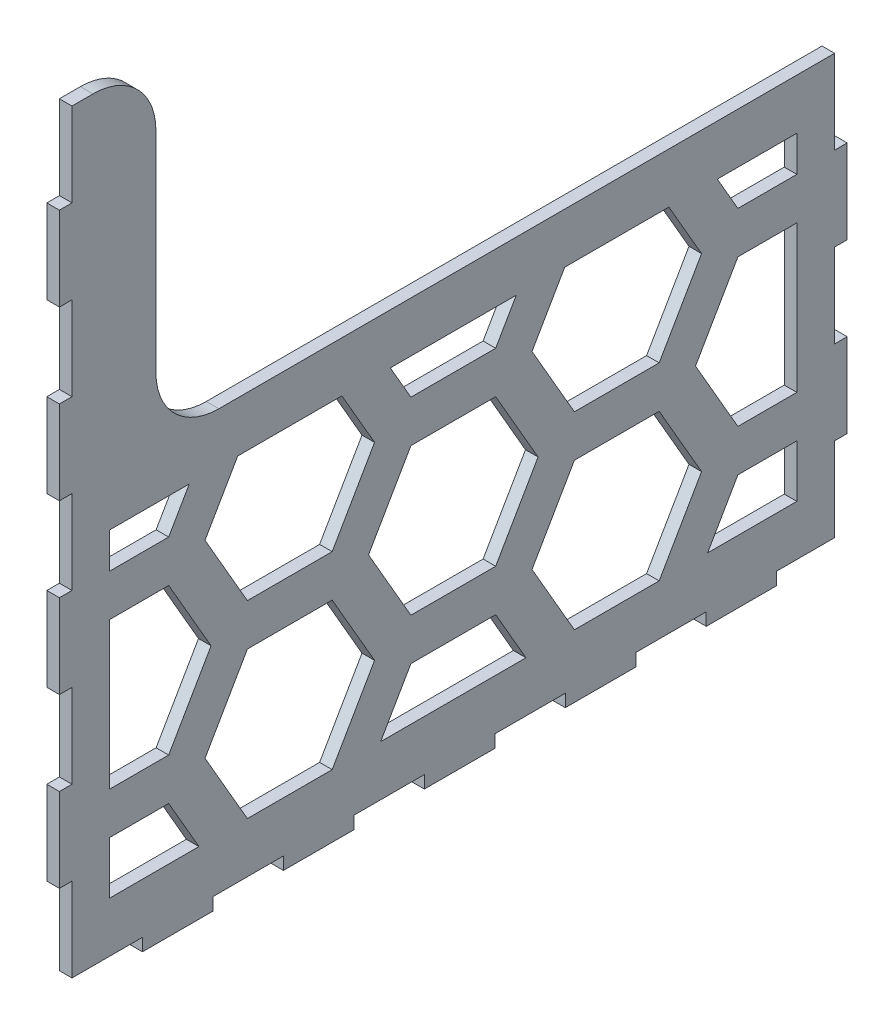
SolidWorks part; units mm, degrees
ref_plane "Front Plane" through (0, 0, 0) normal (0, 0, 1) x (1, 0, 0)
ref_plane "Top Plane" through (0, 0, 0) normal (0, 1, 0) x (1, 0, 0)
ref_plane "Right Plane" through (0, 0, 0) normal (1, 0, 0) x (0, 0, -1)
sketch "Sketch1" plane through (0, 0, 0) normal (1, 0, 0) x (0, 0, -1)
  line L1 (-90.8886, -90) -> (90.8886, -90)
  line L2 (-90.8886, -90) -> (-90.8886, 90)
  line L3 (-90.8886, 90) -> (90.8886, 90)
  line L4 (90.8886, -90) -> (90.8886, 90)
  line L5 (-90.8886, -90) -> (90.8886, 90) construction
  line L6 (-90.8886, 90) -> (90.8886, -90) construction
  point P0 (0, 0)
  dimension "D1" = 181.7773
  dimension "D2" = 180
extrude "Boss-Extrude1" add sketch "Sketch1" along normal blind 3
sketch "Sketch2" plane through (3, 0, 0) normal (1, 0, 0) x (0, 0, -1)
  line L0 (-90.8886, -90) -> (90.8886, -90) construction
  line L1 (-74.0907, -93) -> (-57.2928, -93)
  line L2 (-74.0907, -93) -> (-74.0907, -90)
  line L3 (-74.0907, -90) -> (-57.2928, -90)
  line L4 (-57.2928, -93) -> (-57.2928, -90)
  line L5 (-74.0907, -93) -> (-57.2928, -90) construction
  line L6 (-74.0907, -90) -> (-57.2928, -93) construction
  line L7 (-90.8886, -93) -> (-74.0907, -93) construction
  line L8 (-40.4948, -93) -> (-23.6969, -93)
  line L9 (-40.4948, -93) -> (-40.4948, -90)
  line L10 (-40.4948, -90) -> (-23.6969, -90)
  line L11 (-23.6969, -93) -> (-23.6969, -90)
  line L12 (-40.4948, -93) -> (-23.6969, -90) construction
  line L13 (-40.4948, -90) -> (-23.6969, -93) construction
  line L14 (-6.899, -93) -> (9.899, -93)
  line L15 (-6.899, -93) -> (-6.899, -90)
  line L16 (-6.899, -90) -> (9.899, -90)
  line L17 (9.899, -93) -> (9.899, -90)
  line L18 (-6.899, -93) -> (9.899, -90) construction
  line L19 (-6.899, -90) -> (9.899, -93) construction
  line L20 (-57.2928, -93) -> (-40.4948, -93) construction
  line L21 (-23.6969, -93) -> (-6.899, -93) construction
  line L22 (9.899, -93) -> (26.6969, -93) construction
  line L24 (90.8886, -90) -> (90.8886, 90) construction
  line L25 (93.8886, -70) -> (90.8887, -70)
  line L26 (93.8886, -70) -> (93.8886, -50)
  line L27 (93.8886, -50) -> (90.8886, -50)
  line L28 (90.8887, -70) -> (90.8886, -50)
  line L29 (93.8886, -70) -> (90.8886, -50) construction
  line L30 (93.8886, -50) -> (90.8887, -70) construction
  line L31 (93.8886, 90) -> (93.8886, 70) construction
  line L32 (93.8887, -30) -> (90.8886, -30)
  line L33 (93.8887, -30) -> (93.8886, -10)
  line L34 (93.8886, -10) -> (90.8886, -10)
  line L35 (90.8886, -30) -> (90.8886, -10)
  line L36 (93.8887, -30) -> (90.8886, -10) construction
  line L37 (93.8886, -10) -> (90.8886, -30) construction
  line L38 (93.8887, 10) -> (90.8886, 10)
  line L39 (93.8887, 10) -> (93.8887, 30)
  line L40 (93.8887, 30) -> (90.8886, 30)
  line L41 (90.8886, 10) -> (90.8886, 30)
  line L42 (93.8887, 10) -> (90.8886, 30) construction
  line L43 (93.8887, 30) -> (90.8886, 10) construction
  line L44 (93.8886, 50) -> (90.8886, 50)
  line L45 (93.8886, 50) -> (93.8886, 70)
  line L46 (93.8886, 70) -> (90.8886, 70)
  line L47 (90.8886, 50) -> (90.8886, 70)
  line L48 (93.8886, 50) -> (90.8886, 70) construction
  line L49 (93.8886, 70) -> (90.8886, 50) construction
  line L50 (93.8886, 50) -> (93.8887, 30) construction
  line L51 (93.8887, 10) -> (93.8886, -10) construction
  line L52 (93.8887, -30) -> (93.8886, -50) construction
  line L53 (93.8886, -70) -> (93.8887, -90) construction
  line L54 (90.8886, 90) -> (-90.8886, 90) construction
  line L55 (0, -895.4773) -> (0, 49104.5227) construction
  line L56 (-93.8886, -50) -> (-90.8886, -50)
  line L57 (-90.8887, -70) -> (-90.8886, -50)
  line L58 (-93.8886, -70) -> (-90.8887, -70)
  line L59 (-93.8886, -70) -> (-93.8886, -50)
  line L60 (-93.8886, -10) -> (-90.8886, -10)
  line L61 (-90.8886, -30) -> (-90.8886, -10)
  line L62 (-93.8887, -30) -> (-90.8886, -30)
  line L63 (-93.8887, -30) -> (-93.8886, -10)
  line L64 (-93.8887, 30) -> (-90.8886, 30)
  line L65 (-90.8886, 10) -> (-90.8886, 30)
  line L66 (-93.8887, 10) -> (-90.8886, 10)
  line L67 (-93.8887, 10) -> (-93.8887, 30)
  line L68 (-93.8886, 70) -> (-90.8886, 70)
  line L69 (-90.8886, 50) -> (-90.8886, 70)
  line L70 (-93.8886, 50) -> (-90.8886, 50)
  line L71 (-93.8886, 50) -> (-93.8886, 70)
  line L72 (43.4948, -93) -> (60.2928, -93) construction
  line L73 (43.4948, -93) -> (26.6969, -93)
  line L74 (43.4948, -93) -> (43.4948, -90)
  line L75 (43.4948, -90) -> (26.6969, -90)
  line L76 (26.6969, -93) -> (26.6969, -90)
  line L77 (43.4948, -93) -> (26.6969, -90) construction
  line L78 (43.4948, -90) -> (26.6969, -93) construction
  line L79 (77.0907, -93) -> (60.2928, -93)
  line L80 (77.0907, -93) -> (77.0907, -90)
  line L81 (77.0907, -90) -> (60.2928, -90)
  line L82 (60.2928, -93) -> (60.2928, -90)
  line L83 (77.0907, -93) -> (60.2928, -90) construction
  line L84 (77.0907, -90) -> (60.2928, -93) construction
  line L85 (77.0907, -93) -> (93.8886, -93) construction
  line L86 (-90.8886, 90) -> (-90.8886, -90) construction
  point P0 (-65.6917, -91.5)
  point P7 (-32.0959, -91.5)
  point P12 (1.5, -91.5)
  point P24 (92.3887, -60)
  point P29 (92.3887, -20)
  point P34 (92.3887, 20)
  point P39 (92.3887, 60)
  point P66 (68.6917, -91.5)
  point P75 (35.0959, -91.5)
  dimension "D2" = 3
extrude "Boss-Extrude2" add sketch "Sketch2" against normal up to surface (3 mm away) up to face at (0, 0, 0)
sketch "Sketch3" plane through (3, 0, 0) normal (1, 0, 0) x (0, 0, -1)
  line L4 (93.8887, 10) -> (-70.8886, 10)
  line L6 (-70.8887, 90) -> (93.8886, 90)
  line L7 (93.8886, 90) -> (93.8887, 10)
  line L8 (93.8886, 50) -> (93.8886, 70) construction
  line L9 (90.8886, 10) -> (93.8887, 10) construction
  line L10 (90.8886, 90) -> (-90.8886, 90) construction
  line L11 (-70.8887, 90) -> (-70.8886, 10)
  line L12 (-90.8886, 90) -> (-90.8886, 70) construction
  dimension "D1" = 20
extrude "Cut-Extrude1" cut sketch "Sketch3" against normal through all both and the other way through all
fillet "Fillet1" radius 15 2 edges at (1.5, 10, 70.8886) (1.5, 90, 70.8887)
sketch "Sketch4" plane through (0, 0, 0) normal (-1, 0, 0) x (0, 0, 1)
  line L0 (-145.7809, -20.5) -> (-165.9882, -20.5)
  line L1 (-145.7809, -65.5) -> (-165.9882, -65.5)
  line L2 (-165.9882, -65.5) -> (-176.0918, -83)
  line L3 (-176.0918, -83) -> (-165.9882, -100.5)
  line L4 (-165.9882, -100.5) -> (-145.7809, -100.5)
  line L5 (-145.7809, -100.5) -> (-135.6773, -83)
  line L6 (-135.6773, -83) -> (-145.7809, -65.5)
  line L13 (-165.9882, -20.5) -> (-176.0918, -38)
  line L14 (-137.1207, -105.5) -> (-127.0171, -123)
  line L15 (-127.0171, -123) -> (-106.8098, -123)
  line L16 (-106.8098, -123) -> (-96.7062, -105.5)
  line L17 (-96.7062, -105.5) -> (-106.8098, -88)
  line L18 (-106.8098, -88) -> (-127.0171, -88)
  line L19 (-127.0171, -88) -> (-137.1207, -105.5)
  line L20 (-176.0918, -38) -> (-165.9882, -55.5)
  line L21 (-165.9882, -55.5) -> (-145.7809, -55.5)
  line L22 (-145.7809, -55.5) -> (-135.6773, -38)
  line L23 (-135.6773, -38) -> (-145.7809, -20.5)
  line L24 (-137.1207, -60.5) -> (-127.0171, -78)
  line L25 (-127.0171, -78) -> (-106.8098, -78)
  line L26 (-106.8098, -78) -> (-96.7062, -60.5)
  line L27 (-96.7062, -60.5) -> (-106.8098, -43)
  line L28 (-106.8098, -43) -> (-127.0171, -43)
  line L29 (-127.0171, -43) -> (-137.1207, -60.5)
  line L30 (-145.7809, 24.5) -> (-165.9882, 24.5)
  line L31 (-165.9882, 24.5) -> (-176.0918, 7)
  line L32 (-176.0918, 7) -> (-165.9882, -10.5)
  line L33 (-165.9882, -10.5) -> (-145.7809, -10.5)
  line L34 (-145.7809, -10.5) -> (-135.6773, 7)
  line L35 (-135.6773, 7) -> (-145.7809, 24.5)
  line L36 (-137.1207, -15.5) -> (-127.0171, -33)
  line L37 (-127.0171, -33) -> (-106.8098, -33)
  line L38 (-106.8098, -33) -> (-96.7062, -15.5)
  line L39 (-96.7062, -15.5) -> (-106.8098, 2)
  line L40 (-106.8098, 2) -> (-127.0171, 2)
  line L41 (-127.0171, 2) -> (-137.1207, -15.5)
  line L42 (-145.7809, 69.5) -> (-165.9882, 69.5)
  line L43 (-165.9882, 69.5) -> (-176.0918, 52)
  line L44 (-176.0918, 52) -> (-165.9882, 34.5)
  line L45 (-165.9882, 34.5) -> (-145.7809, 34.5)
  line L46 (-145.7809, 34.5) -> (-135.6773, 52)
  line L47 (-135.6773, 52) -> (-145.7809, 69.5)
  line L48 (-137.1207, 29.5) -> (-127.0171, 12)
  line L49 (-127.0171, 12) -> (-106.8098, 12)
  line L50 (-106.8098, 12) -> (-96.7062, 29.5)
  line L51 (-96.7062, 29.5) -> (-106.8098, 47)
  line L52 (-106.8098, 47) -> (-127.0171, 47)
  line L53 (-127.0171, 47) -> (-137.1207, 29.5)
  line L54 (-145.7809, 114.5) -> (-165.9882, 114.5)
  line L55 (-165.9882, 114.5) -> (-176.0918, 97)
  line L56 (-176.0918, 97) -> (-165.9882, 79.5)
  line L57 (-165.9882, 79.5) -> (-145.7809, 79.5)
  line L58 (-145.7809, 79.5) -> (-135.6773, 97)
  line L59 (-135.6773, 97) -> (-145.7809, 114.5)
  line L60 (-137.1207, 74.5) -> (-127.0171, 57)
  line L61 (-127.0171, 57) -> (-106.8098, 57)
  line L62 (-106.8098, 57) -> (-96.7062, 74.5)
  line L63 (-96.7062, 74.5) -> (-106.8098, 92)
  line L64 (-106.8098, 92) -> (-127.0171, 92)
  line L65 (-127.0171, 92) -> (-137.1207, 74.5)
  line L66 (-145.7809, 159.5) -> (-165.9882, 159.5)
  line L67 (-165.9882, 159.5) -> (-176.0918, 142)
  line L68 (-176.0918, 142) -> (-165.9882, 124.5)
  line L69 (-165.9882, 124.5) -> (-145.7809, 124.5)
  line L70 (-145.7809, 124.5) -> (-135.6773, 142)
  line L71 (-135.6773, 142) -> (-145.7809, 159.5)
  line L72 (-137.1207, 119.5) -> (-127.0171, 102)
  line L73 (-127.0171, 102) -> (-106.8098, 102)
  line L74 (-106.8098, 102) -> (-96.7062, 119.5)
  line L75 (-96.7062, 119.5) -> (-106.8098, 137)
  line L76 (-106.8098, 137) -> (-127.0171, 137)
  line L77 (-127.0171, 137) -> (-137.1207, 119.5)
  line L102 (-145.7809, -65.5) -> (-145.7809, -20.5) construction
  line L103 (-127.0171, -88) -> (-127.0171, -78) construction
  line L104 (-140.7291, -74.25) -> (-132.0689, -69.25) construction
  line L105 (-59.1784, 119.5) -> (-49.0748, 102)
  line L106 (-49.0748, 102) -> (-28.8675, 102)
  line L107 (-28.8675, 102) -> (-18.7639, 119.5)
  line L108 (-18.7639, 119.5) -> (-28.8675, 137)
  line L109 (-28.8675, 137) -> (-49.0748, 137)
  line L110 (-49.0748, 137) -> (-59.1784, 119.5)
  line L111 (-67.8387, 159.5) -> (-88.0459, 159.5)
  line L112 (-88.0459, 159.5) -> (-98.1495, 142)
  line L113 (-98.1495, 142) -> (-88.0459, 124.5)
  line L114 (-88.0459, 124.5) -> (-67.8387, 124.5)
  line L115 (-67.8387, 124.5) -> (-57.735, 142)
  line L116 (-57.735, 142) -> (-67.8387, 159.5)
  line L117 (-67.8387, 114.5) -> (-88.0459, 114.5)
  line L118 (-88.0459, 114.5) -> (-98.1495, 97)
  line L119 (-98.1495, 97) -> (-88.0459, 79.5)
  line L120 (-88.0459, 79.5) -> (-67.8387, 79.5)
  line L121 (-67.8387, 79.5) -> (-57.735, 97)
  line L122 (-57.735, 97) -> (-67.8387, 114.5)
  line L123 (-67.8387, 69.5) -> (-88.0459, 69.5)
  line L124 (-88.0459, 69.5) -> (-98.1495, 52)
  line L125 (-98.1495, 52) -> (-88.0459, 34.5)
  line L126 (-88.0459, 34.5) -> (-67.8387, 34.5)
  line L127 (-67.8387, 34.5) -> (-57.735, 52)
  line L128 (-57.735, 52) -> (-67.8387, 69.5)
  line L129 (-67.8387, 24.5) -> (-88.0459, 24.5)
  line L130 (-88.0459, 24.5) -> (-98.1495, 7)
  line L131 (-98.1495, 7) -> (-88.0459, -10.5)
  line L132 (-88.0459, -10.5) -> (-67.8387, -10.5)
  line L133 (-67.8387, -10.5) -> (-57.735, 7)
  line L134 (-57.735, 7) -> (-67.8387, 24.5)
  line L135 (-59.1784, -15.5) -> (-49.0748, -33)
  line L136 (-49.0748, -33) -> (-28.8675, -33)
  line L137 (-28.8675, -33) -> (-18.7639, -15.5)
  line L138 (-18.7639, -15.5) -> (-28.8675, 2)
  line L139 (-28.8675, 2) -> (-49.0748, 2)
  line L140 (-49.0748, 2) -> (-59.1784, -15.5)
  line L141 (-67.8387, -20.5) -> (-88.0459, -20.5)
  line L142 (-88.0459, -20.5) -> (-98.1495, -38)
  line L143 (-98.1495, -38) -> (-88.0459, -55.5)
  line L144 (-88.0459, -55.5) -> (-67.8387, -55.5)
  line L145 (-67.8387, -55.5) -> (-57.735, -38)
  line L146 (-57.735, -38) -> (-67.8387, -20.5)
  line L147 (-59.1784, -60.5) -> (-49.0748, -78)
  line L148 (-49.0748, -78) -> (-28.8675, -78)
  line L149 (-28.8675, -78) -> (-18.7639, -60.5)
  line L150 (-18.7639, -60.5) -> (-28.8675, -43)
  line L151 (-28.8675, -43) -> (-49.0748, -43)
  line L152 (-49.0748, -43) -> (-59.1784, -60.5)
  line L153 (-67.8387, -65.5) -> (-88.0459, -65.5)
  line L154 (-88.0459, -65.5) -> (-98.1495, -83)
  line L155 (-98.1495, -83) -> (-88.0459, -100.5)
  line L156 (-88.0459, -100.5) -> (-67.8387, -100.5)
  line L157 (-67.8387, -100.5) -> (-57.735, -83)
  line L158 (-57.735, -83) -> (-67.8387, -65.5)
  line L159 (-59.1784, -105.5) -> (-49.0748, -123)
  line L160 (-49.0748, -123) -> (-28.8675, -123)
  line L161 (-28.8675, -123) -> (-18.7639, -105.5)
  line L162 (-18.7639, -105.5) -> (-28.8675, -88)
  line L163 (-28.8675, -88) -> (-49.0748, -88)
  line L164 (-49.0748, -88) -> (-59.1784, -105.5)
  line L165 (-59.1784, 29.5) -> (-49.0748, 12)
  line L166 (-49.0748, 12) -> (-28.8675, 12)
  line L167 (-28.8675, 12) -> (-18.7639, 29.5)
  line L168 (-18.7639, 29.5) -> (-28.8675, 47)
  line L169 (-28.8675, 47) -> (-49.0748, 47)
  line L170 (-49.0748, 47) -> (-59.1784, 29.5)
  line L171 (-59.1784, 74.5) -> (-49.0748, 57)
  line L172 (-49.0748, 57) -> (-28.8675, 57)
  line L173 (-28.8675, 57) -> (-18.7639, 74.5)
  line L174 (-18.7639, 74.5) -> (-28.8675, 92)
  line L175 (-28.8675, 92) -> (-49.0748, 92)
  line L176 (-49.0748, 92) -> (-59.1784, 74.5)
  line L177 (18.7639, 119.5) -> (28.8675, 102)
  line L178 (28.8675, 102) -> (49.0748, 102)
  line L179 (49.0748, 102) -> (59.1784, 119.5)
  line L180 (59.1784, 119.5) -> (49.0748, 137)
  line L181 (49.0748, 137) -> (28.8675, 137)
  line L182 (28.8675, 137) -> (18.7639, 119.5)
  line L183 (10.1036, 159.5) -> (-10.1036, 159.5)
  line L184 (-10.1036, 159.5) -> (-20.2073, 142)
  line L185 (-20.2073, 142) -> (-10.1036, 124.5)
  line L186 (-10.1036, 124.5) -> (10.1036, 124.5)
  line L187 (10.1036, 124.5) -> (20.2073, 142)
  line L188 (20.2073, 142) -> (10.1036, 159.5)
  line L189 (10.1036, 114.5) -> (-10.1036, 114.5)
  line L190 (-10.1036, 114.5) -> (-20.2073, 97)
  line L191 (-20.2073, 97) -> (-10.1036, 79.5)
  line L192 (-10.1036, 79.5) -> (10.1036, 79.5)
  line L193 (10.1036, 79.5) -> (20.2073, 97)
  line L194 (20.2073, 97) -> (10.1036, 114.5)
  line L195 (10.1036, 69.5) -> (-10.1036, 69.5)
  line L196 (-10.1036, 69.5) -> (-20.2073, 52)
  line L197 (-20.2073, 52) -> (-10.1036, 34.5)
  line L198 (-10.1036, 34.5) -> (10.1036, 34.5)
  line L199 (10.1036, 34.5) -> (20.2073, 52)
  line L200 (20.2073, 52) -> (10.1036, 69.5)
  line L201 (10.1036, 24.5) -> (-10.1036, 24.5)
  line L202 (-10.1036, 24.5) -> (-20.2073, 7)
  line L203 (-20.2073, 7) -> (-10.1036, -10.5)
  line L204 (-10.1036, -10.5) -> (10.1036, -10.5)
  line L205 (10.1036, -10.5) -> (20.2073, 7)
  line L206 (20.2073, 7) -> (10.1036, 24.5)
  line L207 (18.7639, -15.5) -> (28.8675, -33)
  line L208 (28.8675, -33) -> (49.0748, -33)
  line L209 (49.0748, -33) -> (59.1784, -15.5)
  line L210 (59.1784, -15.5) -> (49.0748, 2)
  line L211 (49.0748, 2) -> (28.8675, 2)
  line L212 (28.8675, 2) -> (18.7639, -15.5)
  line L213 (10.1036, -20.5) -> (-10.1036, -20.5)
  line L214 (-10.1036, -20.5) -> (-20.2073, -38)
  line L215 (-20.2073, -38) -> (-10.1036, -55.5)
  line L216 (-10.1036, -55.5) -> (10.1036, -55.5)
  line L217 (10.1036, -55.5) -> (20.2073, -38)
  line L218 (20.2073, -38) -> (10.1036, -20.5)
  line L219 (18.7639, -60.5) -> (28.8675, -78)
  line L220 (28.8675, -78) -> (49.0748, -78)
  line L221 (49.0748, -78) -> (59.1784, -60.5)
  line L222 (59.1784, -60.5) -> (49.0748, -43)
  line L223 (49.0748, -43) -> (28.8675, -43)
  line L224 (28.8675, -43) -> (18.7639, -60.5)
  line L225 (10.1036, -65.5) -> (-10.1036, -65.5)
  line L226 (-10.1036, -65.5) -> (-20.2073, -83)
  line L227 (-20.2073, -83) -> (-10.1036, -100.5)
  line L228 (-10.1036, -100.5) -> (10.1036, -100.5)
  line L229 (10.1036, -100.5) -> (20.2073, -83)
  line L230 (20.2073, -83) -> (10.1036, -65.5)
  line L231 (18.7639, -105.5) -> (28.8675, -123)
  line L232 (28.8675, -123) -> (49.0748, -123)
  line L233 (49.0748, -123) -> (59.1784, -105.5)
  line L234 (59.1784, -105.5) -> (49.0748, -88)
  line L235 (49.0748, -88) -> (28.8675, -88)
  line L236 (28.8675, -88) -> (18.7639, -105.5)
  line L237 (18.7639, 29.5) -> (28.8675, 12)
  line L238 (28.8675, 12) -> (49.0748, 12)
  line L239 (49.0748, 12) -> (59.1784, 29.5)
  line L240 (59.1784, 29.5) -> (49.0748, 47)
  line L241 (49.0748, 47) -> (28.8675, 47)
  line L242 (28.8675, 47) -> (18.7639, 29.5)
  line L243 (18.7639, 74.5) -> (28.8675, 57)
  line L244 (28.8675, 57) -> (49.0748, 57)
  line L245 (49.0748, 57) -> (59.1784, 74.5)
  line L246 (59.1784, 74.5) -> (49.0748, 92)
  line L247 (49.0748, 92) -> (28.8675, 92)
  line L248 (28.8675, 92) -> (18.7639, 74.5)
  line L249 (96.7062, 119.5) -> (106.8098, 102)
  line L250 (106.8098, 102) -> (127.0171, 102)
  line L251 (127.0171, 102) -> (137.1207, 119.5)
  line L252 (137.1207, 119.5) -> (127.0171, 137)
  line L253 (127.0171, 137) -> (106.8098, 137)
  line L254 (106.8098, 137) -> (96.7062, 119.5)
  line L255 (88.0459, 159.5) -> (67.8387, 159.5)
  line L256 (67.8387, 159.5) -> (57.735, 142)
  line L257 (57.735, 142) -> (67.8387, 124.5)
  line L258 (67.8387, 124.5) -> (88.0459, 124.5)
  line L259 (88.0459, 124.5) -> (98.1495, 142)
  line L260 (98.1495, 142) -> (88.0459, 159.5)
  line L261 (88.0459, 114.5) -> (67.8387, 114.5)
  line L262 (67.8387, 114.5) -> (57.735, 97)
  line L263 (57.735, 97) -> (67.8387, 79.5)
  line L264 (67.8387, 79.5) -> (88.0459, 79.5)
  line L265 (88.0459, 79.5) -> (98.1495, 97)
  line L266 (98.1495, 97) -> (88.0459, 114.5)
  line L267 (88.0459, 69.5) -> (67.8387, 69.5)
  line L268 (67.8387, 69.5) -> (57.735, 52)
  line L269 (57.735, 52) -> (67.8387, 34.5)
  line L270 (67.8387, 34.5) -> (88.0459, 34.5)
  line L271 (88.0459, 34.5) -> (98.1495, 52)
  line L272 (98.1495, 52) -> (88.0459, 69.5)
  line L273 (88.0459, 24.5) -> (67.8387, 24.5)
  line L274 (67.8387, 24.5) -> (57.735, 7)
  line L275 (57.735, 7) -> (67.8387, -10.5)
  line L276 (67.8387, -10.5) -> (88.0459, -10.5)
  line L277 (88.0459, -10.5) -> (98.1495, 7)
  line L278 (98.1495, 7) -> (88.0459, 24.5)
  line L279 (96.7062, -15.5) -> (106.8098, -33)
  line L280 (106.8098, -33) -> (127.0171, -33)
  line L281 (127.0171, -33) -> (137.1207, -15.5)
  line L282 (137.1207, -15.5) -> (127.0171, 2)
  line L283 (127.0171, 2) -> (106.8098, 2)
  line L284 (106.8098, 2) -> (96.7062, -15.5)
  line L285 (88.0459, -20.5) -> (67.8387, -20.5)
  line L286 (67.8387, -20.5) -> (57.735, -38)
  line L287 (57.735, -38) -> (67.8387, -55.5)
  line L288 (67.8387, -55.5) -> (88.0459, -55.5)
  line L289 (88.0459, -55.5) -> (98.1495, -38)
  line L290 (98.1495, -38) -> (88.0459, -20.5)
  line L291 (96.7062, -60.5) -> (106.8098, -78)
  line L292 (106.8098, -78) -> (127.0171, -78)
  line L293 (127.0171, -78) -> (137.1207, -60.5)
  line L294 (137.1207, -60.5) -> (127.0171, -43)
  line L295 (127.0171, -43) -> (106.8098, -43)
  line L296 (106.8098, -43) -> (96.7062, -60.5)
  line L297 (88.0459, -65.5) -> (67.8387, -65.5)
  line L298 (67.8387, -65.5) -> (57.735, -83)
  line L299 (57.735, -83) -> (67.8387, -100.5)
  line L300 (67.8387, -100.5) -> (88.0459, -100.5)
  line L301 (88.0459, -100.5) -> (98.1495, -83)
  line L302 (98.1495, -83) -> (88.0459, -65.5)
  line L303 (96.7062, -105.5) -> (106.8098, -123)
  line L304 (106.8098, -123) -> (127.0171, -123)
  line L305 (127.0171, -123) -> (137.1207, -105.5)
  line L306 (137.1207, -105.5) -> (127.0171, -88)
  line L307 (127.0171, -88) -> (106.8098, -88)
  line L308 (106.8098, -88) -> (96.7062, -105.5)
  line L309 (96.7062, 29.5) -> (106.8098, 12)
  line L310 (106.8098, 12) -> (127.0171, 12)
  line L311 (127.0171, 12) -> (137.1207, 29.5)
  line L312 (137.1207, 29.5) -> (127.0171, 47)
  line L313 (127.0171, 47) -> (106.8098, 47)
  line L314 (106.8098, 47) -> (96.7062, 29.5)
  line L315 (96.7062, 74.5) -> (106.8098, 57)
  line L316 (106.8098, 57) -> (127.0171, 57)
  line L317 (127.0171, 57) -> (137.1207, 74.5)
  line L318 (137.1207, 74.5) -> (127.0171, 92)
  line L319 (127.0171, 92) -> (106.8098, 92)
  line L320 (106.8098, 92) -> (96.7062, 74.5)
  line L321 (-137.1207, 119.5) -> (-59.1784, 119.5) construction
  line L322 (-93.0977, -74.25) -> (-101.758, -69.25) construction
  line L323 (-93.8887, -30) -> (-93.8886, -10) construction
  line L324 (-81.8887, -78) -> (81.8887, -78)
  line L325 (-81.8887, -78) -> (-81.8887, 78)
  line L326 (-81.8887, 78) -> (81.8887, 78)
  line L327 (81.8887, -78) -> (81.8887, 78)
  line L328 (-81.8887, -78) -> (81.8887, 78) construction
  line L329 (-81.8887, 78) -> (81.8887, -78) construction
  line L330 (23.6969, -90) -> (6.899, -90) construction
  line L331 (-106.8098, -43) -> (-81.8887, -43) construction
  line L332 (106.8098, -43) -> (81.8887, -43) construction
  line L333 (-81.8887, -2) -> (81.8887, -2)
  line L334 (55.8886, 10) -> (-90.8886, 10) construction
  circle A0 centre (-155.8846, -83) radius 17.5 construction
  circle A1 centre (-116.9134, -105.5) radius 17.5 construction
  point P10 (-127.0171, -83)
  point P301 (0, 0)
  dimension "D3" = 35
  dimension "D2" = 45
  dimension "D5" = 12
  dimension "D6" = 12
  dimension "D7" = 12
  dimension "D1" = 6
  dimension "D4" = 4
extrude "Cut-Extrude2" cut sketch "Sketch4" against normal blind 10 contours L324 L325 L153 L158 | L152 L151 L150 L149 L148 L147 | L324 L226 L225 L230 | L224 L223 L222 L221 L220 L219 | L327 L324 L298 L297 | L327 L288 L287 L286 L285 | L212 L333 L210 L209 L208 L207 | L275 L333 L327 L276 | L218 L217 L216 L215 L214 L213 | L203 L333 L205 L204 | L140 L333 L138 L137 L136 L135 | L144 L325 L141 L146 L145 | L325 L333 L133 L132
